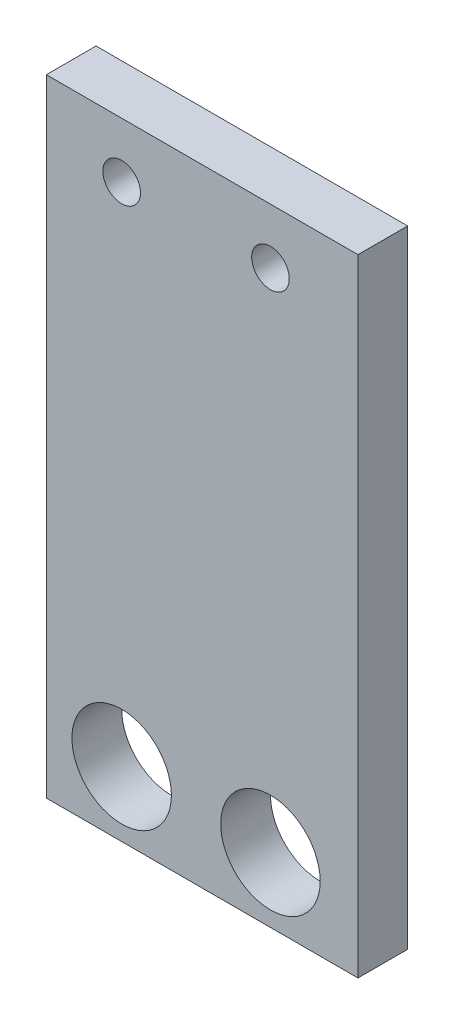
SolidWorks part; units mm, degrees
ref_plane "Front Plane" through (0, 0, 0) normal (0, 0, 1) x (1, 0, 0)
ref_plane "Top Plane" through (0, 0, 0) normal (0, 1, 0) x (1, 0, 0)
ref_plane "Right Plane" through (0, 0, 0) normal (1, 0, 0) x (0, 0, -1)
sketch "Sketch1" plane through (0, 0, 0) normal (0, 0, 1) x (1, 0, 0)
  line L1 (-9.046, 15.7038) -> (10.854, 15.7038)
  line L2 (-9.046, 15.7038) -> (-9.046, -24.2962)
  line L3 (-9.046, -24.2962) -> (10.854, -24.2962)
  line L4 (10.854, 15.7038) -> (10.854, -24.2962)
  circle A0 centre (-4.234, 12.1721) radius 1.2
  circle A1 centre (5.266, 12.1721) radius 1.2
  circle A2 centre (-4.234, -20.1518) radius 3.175
  circle A3 centre (5.266, -20.1518) radius 3.175
  dimension "D3" = 2.4
  dimension "D4" = 2.4
  dimension "D6" = 5.588
  dimension "D7" = 6.35
  dimension "D8" = 6.35
  dimension "D1" = 19.9
  dimension "D2" = 40
  dimension "D5" = 9.5
extrude "Boss-Extrude1" add sketch "Sketch1" along normal blind 3.175
